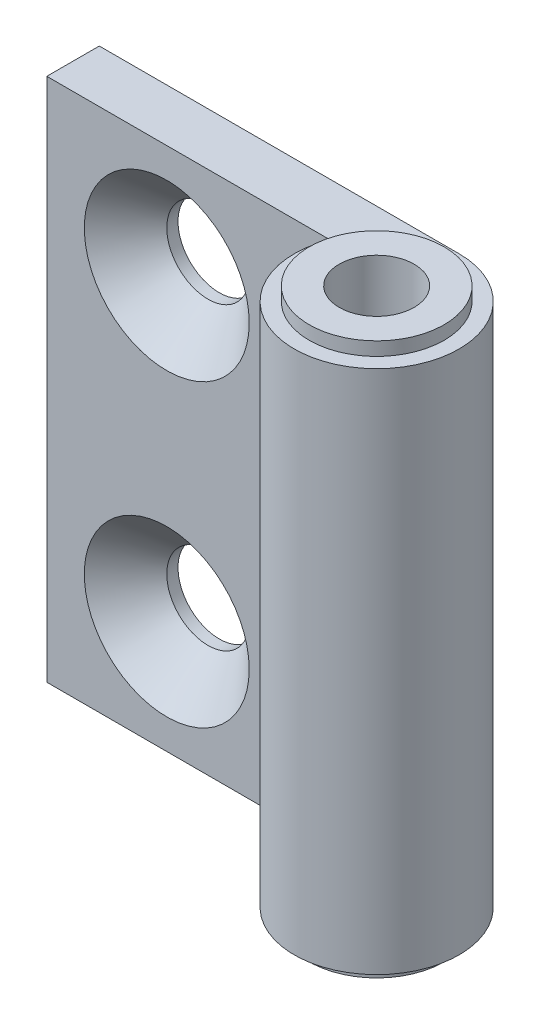
SolidWorks part; units mm, degrees
ref_plane "Piano frontale" through (0, 0, 0) normal (0, 0, 1) x (1, 0, 0)
ref_plane "Piano superiore" through (0, 0, 0) normal (0, 1, 0) x (1, 0, 0)
ref_plane "Piano destro" through (0, 0, 0) normal (1, 0, 0) x (0, 0, -1)
ref_plane "Plane1" through (0, 35.9, 0) normal (0, 1, 0) x (1, 0, 0)
sketch "Sketch1" plane through (0, 35.9, 0) normal (0, 1, 0) x (1, 0, 0)
  line L0 (-24, 5.5) -> (-24, 2)
  line L1 (-24, 2) -> (-5.1235, 2)
  line L2 (0, 5.5) -> (-24, 5.5)
  arc A0 (-5.1235, 2) -> (0, 5.5) centre (0, 0) ccw
extrude "Extrude1" add sketch "Sketch1" against normal blind 35
sketch "Sketch2" plane through (0, 0, 0) normal (0, 0, 1) x (1, 0, 0)
  line L0 (4.5, 0.9) -> (0, 0.9)
  line L1 (0, 0.9) -> (0, 0)
  line L2 (0, 0) -> (4.5, 0)
  line L3 (4.5, 0) -> (4.5, 0.9)
  line L4 (0, 0.9) -> (0, 0) construction
revolve "Revolve1" add sketch "Sketch2" angle 360 about L4
sketch "Sketch3" plane through (0, 0, 0) normal (0, 0, 1) x (1, 0, 0)
  line L0 (4.5, 36.8) -> (0, 36.8)
  line L1 (0, 36.8) -> (0, 35.9)
  line L2 (0, 35.9) -> (4.5, 35.9)
  line L3 (4.5, 35.9) -> (4.5, 36.8)
  line L4 (0, 36.8) -> (0, 35.9) construction
revolve "Revolve2" add sketch "Sketch3" angle 360 about L4
hole_wizard "HoleWzd1" positions "Sketch5" profile "Sketch4" countersink size "M5" standard "Ansi Metric"
sketch "Sketch5" plane through (0, 0, -2) normal (0, 0, 1) x (1, 0, 0)
  point P0 (-16, 28.4)
  point P1 (-16, 8.4)
sketch "Sketch4" plane through (-16, 28.4, -2) normal (1, 0, 0) x (0, -1, 0)
  line L0 (0, 0) -> (0, 3.5)
  line L1 (0, 3.5) -> (2.75, 3.5)
  line L2 (2.75, 3.5) -> (2.75, 2.75)
  line L3 (2.75, 2.75) -> (5.5, 0)
  line L5 (5.5, 0) -> (0, 0)
  line L6 (-2.75, 2.75) -> (-5.5, 0) construction
  line L11 (0, -6.35) -> (0, 107.95) construction
  dimension "Thru Hole Dia." = 5.5
  dimension "Thru Hole Depth" = 3.5
  dimension "Near C'Sink Dia." = 11
  dimension "Near C'Sink Angle" = 90
hole_wizard "HoleWzd2" positions "Sketch7" profile "Sketch6" hole size "Ø5.0" standard "Ansi Metric"
sketch "Sketch7" plane through (0, 36.8, 0) normal (0, 1, 0) x (1, 0, 0)
  point P0 (0, 0)
sketch "Sketch6" plane through (0, 36.8, 0) normal (1, 0, 0) x (0, 0, 1)
  line L0 (0, 0) -> (0, 36.8)
  line L1 (0, 36.8) -> (2.5, 36.8)
  line L2 (2.5, 36.8) -> (2.5, 0)
  line L5 (2.5, 0) -> (0, 0)
  line L11 (0, -6.35) -> (0, 107.95) construction
  dimension "Thru Hole Dia." = 5
  dimension "Thru Hole Depth" = 36.8
